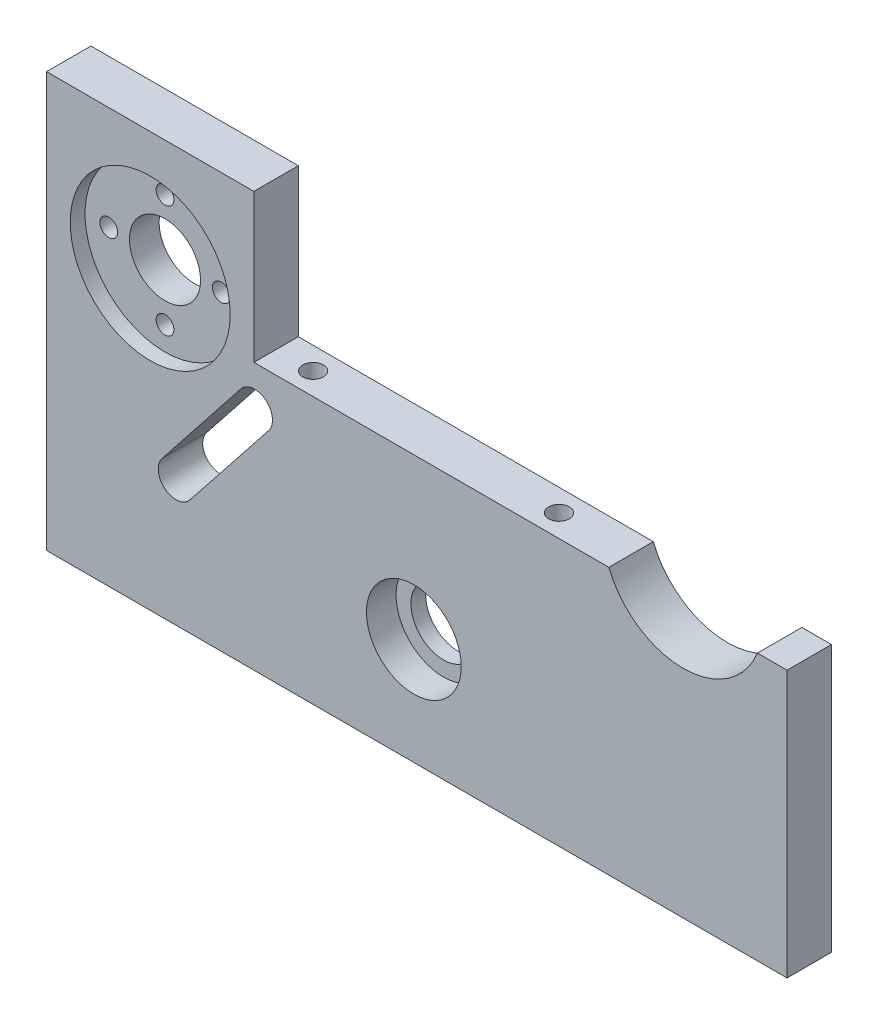
SolidWorks part; units mm, degrees
ref_plane "Plan de face" through (0, 0, 0) normal (0, 0, 1) x (1, 0, 0)
ref_plane "Plan de dessus" through (0, 0, 0) normal (0, 1, 0) x (1, 0, 0)
ref_plane "Plan de droite" through (0, 0, 0) normal (1, 0, 0) x (0, 0, -1)
sketch "Esquisse1" plane through (0, 0, 0) normal (0, 0, 1) x (1, 0, 0)
  line L0 (-53.3856, 37.6711) -> (-53.3856, -32.3289)
  line L1 (-53.3856, -32.3289) -> (71.6144, -32.3289)
  line L2 (71.6144, -32.3289) -> (71.6144, 12.6711)
  line L3 (71.6144, 12.6711) -> (-18.3856, 12.6711)
  line L4 (-18.3856, 12.6711) -> (-18.3856, 37.6711)
  line L5 (-18.3856, 37.6711) -> (-53.3856, 37.6711)
  dimension "D1" = 35
  dimension "D2" = 70
  dimension "D3" = 125
  dimension "D4" = 45
extrude "Boss.-Extru.1" add sketch "Esquisse1" along normal blind 7.5
sketch "Esquisse2" plane through (0, 0, 7.5) normal (0, 0, 1) x (1, 0, 0)
  line L0 (-18.3856, 37.6711) -> (-53.3856, 37.6711) construction
  line L1 (-49.3856, 17.6711) -> (-53.3856, 17.6711) construction
  line L4 (-53.3856, 37.6711) -> (-53.3856, -32.3289) construction
  circle A0 centre (-35.8856, 17.6711) radius 13.5
  point P12 (0, 0)
  dimension "D1" = 27
  dimension "D2" = 20
  dimension "D3" = 4
sketch "Esquisse3" plane through (0, 0, 0) normal (0, 0, -1) x (-1, 0, 0)
  line L0 (35.8856, 31.1711) -> (35.8856, 4.1711) construction
  line L1 (53.3856, 37.6711) -> (53.3856, -32.3289) construction
  line L2 (18.3856, 37.6711) -> (53.3856, 37.6711) construction
  circle A5 centre (45.3856, 17.6711) radius 1.5
  circle A9 centre (35.8856, 17.6711) radius 13.5 construction
  circle A10 centre (35.8856, 17.6711) radius 6
  circle A11 centre (35.8856, 8.1711) radius 1.5
  circle A12 centre (35.8856, 17.6711) radius 6
  circle A13 centre (26.3856, 17.6711) radius 1.5
  circle A14 centre (35.8856, 17.6711) radius 6
  circle A15 centre (35.8856, 27.1711) radius 1.5
  circle A16 centre (35.8856, 17.6711) radius 6
  point P14 (35.8856, 17.6711)
  point P24 (35.8856, 17.6711)
  dimension "D1" = 8
  dimension "D3" = 12
  dimension "D2" = 3
  dimension "D5" = 20
  dimension "D6" = 9.5
  dimension "D4" = 4
sketch "Esquisse4" plane through (0, 0, 7.5) normal (0, 0, 1) x (1, 0, 0)
  line L0 (71.6144, 12.6711) -> (-18.3856, 12.6711) construction
  line L1 (41.5345, 12.6711) -> (66.6144, 12.6711)
  line L3 (54.0745, 4.1711) -> (54.0745, 21.913) construction
  line L4 (-35.8856, 4.1711) -> (54.0745, 4.1711) construction
  line L5 (-20.5995, 7.6785) -> (-33.8781, -9.115)
  line L6 (-15.893, 3.9571) -> (-29.1716, -12.8364)
  line L10 (71.6144, -32.3289) -> (71.6144, 12.6711) construction
  line L11 (-53.3856, -32.3289) -> (71.6144, -32.3289) construction
  line L14 (-53.3856, 37.6711) -> (-53.3856, -32.3289) construction
  arc A0 (66.6144, 12.6711) -> (41.5345, 12.6711) centre (54.0745, 17.6711) cw
  arc A7 (-20.5995, 7.6785) -> (-15.893, 3.9571) centre (-18.2463, 5.8178) cw
  arc A9 (-33.8781, -9.115) -> (-29.1716, -12.8364) centre (-31.5249, -10.9757) ccw
  point P16 (-33.3856, -13.3289)
  point P21 (-16.3856, 8.1711)
  point P24 (-53.3856, -13.4053)
  dimension "D2" = 13.5
  dimension "D4" = 6
  dimension "D1" = 5
  dimension "D5" = 19
  dimension "D6" = 20
  dimension "D7" = 4.5
  dimension "D8" = 88
extrude "Repose moteur" cut sketch "Esquisse4" against normal blind 8
sketch "Esquisse5" plane through (0, 0, 7.5) normal (0, 0, 1) x (1, 0, 0)
  line L0 (16.6144, -14.3289) -> (71.6144, -14.3289) construction
  line L1 (71.6144, -32.3289) -> (71.6144, 12.6711) construction
  line L4 (-53.3856, -32.3289) -> (71.6144, -32.3289) construction
  line L5 (8.6144, -14.3289) -> (8.6144, 21.228) construction
  circle A0 centre (8.6144, -14.3289) radius 8
  dimension "D2" = 16
  dimension "D1" = 55
  dimension "D3" = 18
sketch "Esquisse6" plane through (0, 0, 0) normal (0, 0, -1) x (-1, 0, 0)
  circle A0 centre (-8.6144, -14.3289) radius 5.5
  dimension "D1" = 11
extrude "Fixation courroi 1" cut sketch "Esquisse5" against normal blind 5
extrude "Fixation courroi 2" cut sketch "Esquisse6" against normal blind 2.5
extrude "Fixation moteur 1" cut sketch "Esquisse3" against normal blind 5 contours A13 | A15 L0 | L0 A15 | A5 | A11 L0 | L0 A11 | L0 A10 | A16 L0
extrude "Fixation moteur 2" cut sketch "Esquisse2" against normal blind 2.5
sketch "Esquisse7" plane through (0, -32.3289, 0) normal (0, -1, 0) x (1, 0, 0)
  line L0 (-53.3856, 7.5) -> (-53.3856, 0) construction
  line L1 (71.6144, 7.5) -> (71.6144, 0) construction
  circle A0 centre (-49.3856, 3.8003) radius 1.75
  circle A1 centre (-17.8856, 3.8003) radius 1.75
  circle A2 centre (36.1144, 3.8003) radius 1.75
  circle A3 centre (67.6144, 3.8003) radius 1.75
  dimension "D5" = 3.5
  dimension "D6" = 3.5
  dimension "D7" = 3.5
  dimension "D8" = 3.5
  dimension "D1" = 4
  dimension "D2" = 31.5
  dimension "D3" = 4
  dimension "D4" = 31.5
sketch "Esquisse9" plane through (0, 12.6711, 0) normal (0, 1, 0) x (1, 0, 0)
  line L0 (8.6144, -7.5) -> (8.6144, 0) construction
  line L1 (0.6144, -7.5) -> (16.6144, -7.5) construction
  line L2 (41.5345, 0) -> (-18.3856, 0) construction
  line L3 (8.6144, -3.75) -> (-12.1356, -3.75) construction
  line L4 (8.6144, -3.75) -> (29.3644, -3.75) construction
  circle A0 centre (-12.1356, -3.75) radius 1.75
  circle A1 centre (29.3644, -3.75) radius 1.75
  dimension "D1" = 3.5
  dimension "D2" = 3.5
  dimension "D3" = 41.5
extrude "Percage 1" cut sketch "Esquisse9" against normal blind 7
extrude "Percage 2" cut sketch "Esquisse7" against normal blind 7
